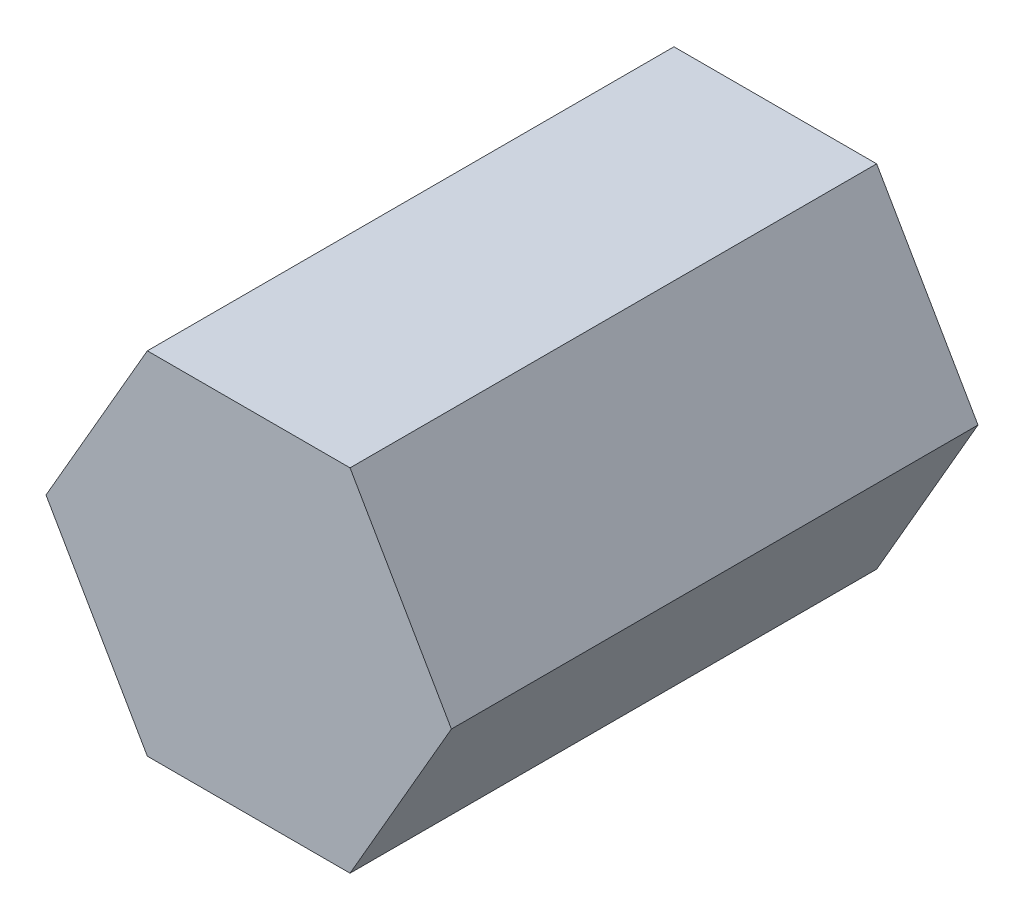
SolidWorks part; units mm, degrees
material "ABS"
ref_plane "Front Plane" through (0, 0, 0) normal (0, 0, 1) x (1, 0, 0)
ref_plane "Top Plane" through (0, 0, 0) normal (0, 1, 0) x (1, 0, 0)
ref_plane "Right Plane" through (0, 0, 0) normal (1, 0, 0) x (0, 0, -1)
sketch "Sketch1" plane through (0, 0, 0) normal (0, 0, 1) x (1, 0, 0)
  line L1 (14.4338, 25) -> (-14.4338, 25)
  line L2 (-14.4338, 25) -> (-28.8675, 0)
  line L3 (-28.8675, 0) -> (-14.4338, -25)
  line L4 (-14.4338, -25) -> (14.4338, -25)
  line L5 (14.4338, -25) -> (28.8675, 0)
  line L6 (28.8675, 0) -> (14.4338, 25)
  circle A0 centre (0, 0) radius 25 construction
  point P1 (0, 0)
  point P10 (0, 0)
  dimension "D1" = 50
extrude "Boss-Extrude1" add sketch "Sketch1" along normal mid plane 75
ref_point "Point1"
